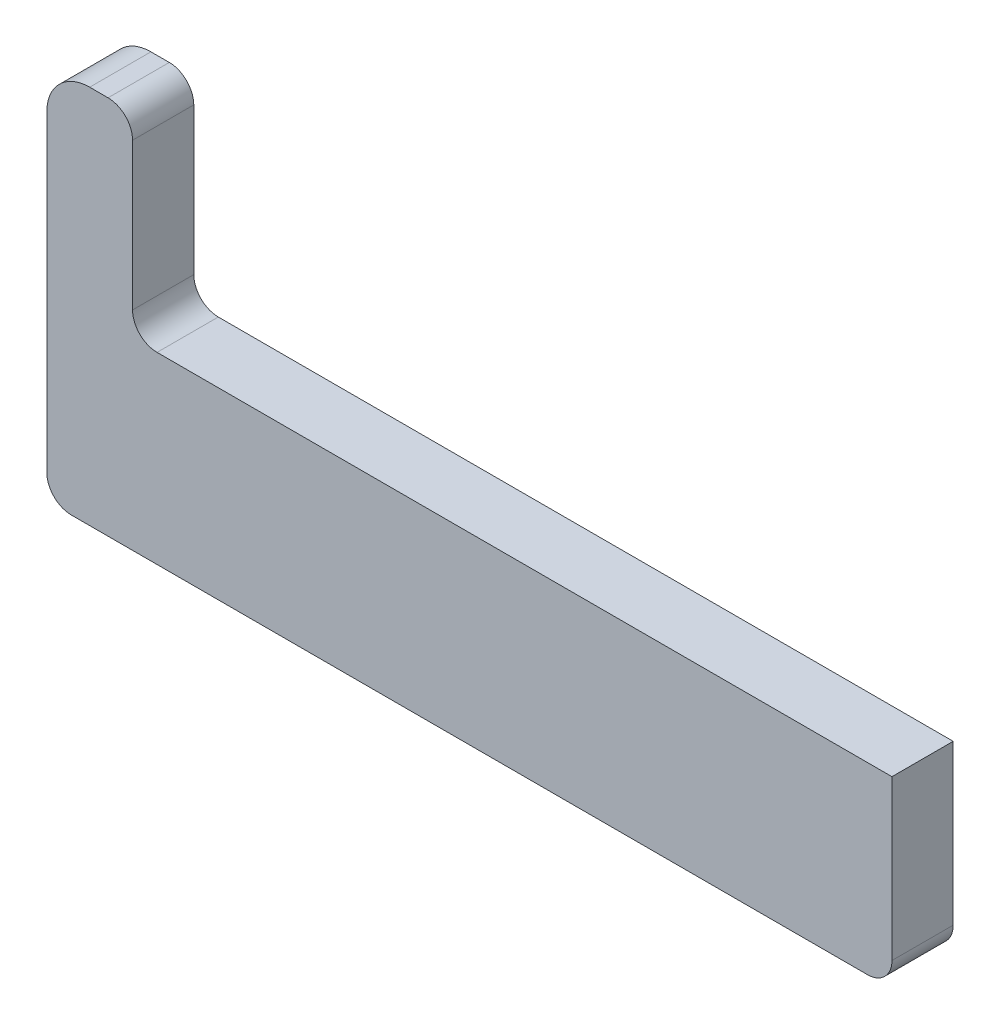
SolidWorks part; units mm, degrees
ref_plane "Plan de face" through (0, 0, 0) normal (0, 0, 1) x (1, 0, 0)
ref_plane "Plan de dessus" through (0, 0, 0) normal (0, 1, 0) x (1, 0, 0)
ref_plane "Plan de droite" through (0, 0, 0) normal (1, 0, 0) x (0, 0, -1)
sketch "Esquisse1" plane through (0, 0, 0) normal (0, 0, 1) x (1, 0, 0)
  line L0 (-2, 0) -> (-67, 0)
  line L1 (-69, 2) -> (-69, 27.5)
  line L2 (-65.5, 31) -> (-64, 31)
  line L3 (-62, 29) -> (-62, 17)
  line L4 (-60, 15) -> (0, 15)
  line L5 (0, 15) -> (0, 2)
  arc A0 (-69, 27.5) -> (-65.5, 31) centre (-65.5, 27.5) cw
  arc A1 (-67, 0) -> (-69, 2) centre (-67, 2) cw
  arc A2 (-2, 0) -> (0, 2) centre (-2, 2) ccw
  arc A3 (-62, 17) -> (-60, 15) centre (-60, 17) ccw
  arc A4 (-64, 31) -> (-62, 29) centre (-64, 29) cw
  point P9 (-69, 31)
  point P12 (-69, 0)
  point P15 (0, 0)
  point P20 (-62, 31)
  dimension "D5" = 3.5
  dimension "D6" = 2
  dimension "D1" = 69
  dimension "D2" = 7
  dimension "D3" = 15
  dimension "D4" = 31
extrude "Boss.-Extru.1" add sketch "Esquisse1" along normal blind 5
